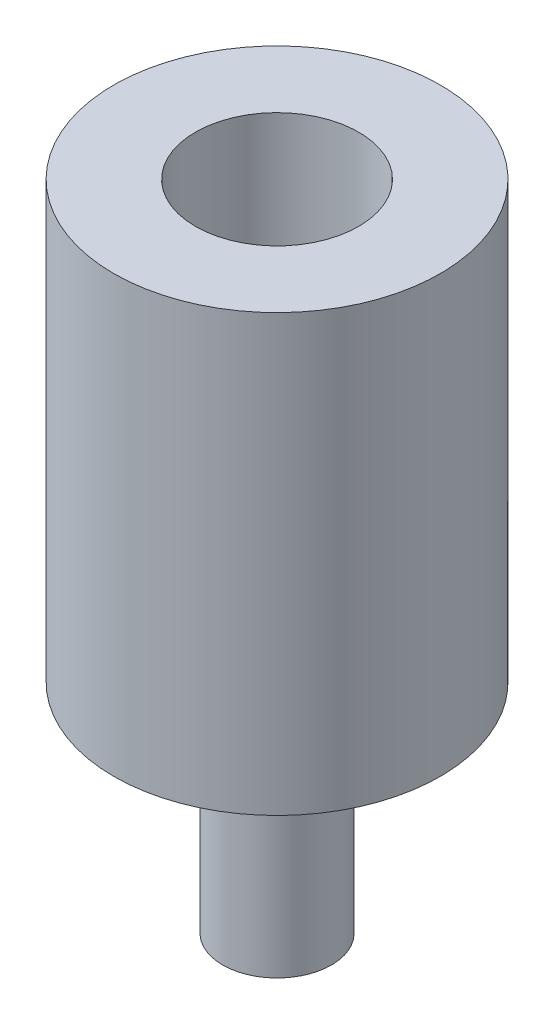
SolidWorks part; units mm, degrees
ref_plane "Front Plane" through (0, 0, 0) normal (0, 0, 1) x (1, 0, 0)
ref_plane "Top Plane" through (0, 0, 0) normal (0, 1, 0) x (1, 0, 0)
ref_plane "Right Plane" through (0, 0, 0) normal (1, 0, 0) x (0, 0, -1)
sketch "Sketch1" plane through (0, 0, 0) normal (0, 1, 0) x (1, 0, 0)
  circle A0 centre (0, 0) radius 2.5
  dimension "D1" = 5
extrude "Boss-Extrude2" add sketch "Sketch1" along normal blind 10
ref_plane "Plane1" through (0, 10, 0) normal (0, 1, 0) x (1, 0, 0)
sketch "Sketch2" plane through (0, 10, 0) normal (0, 1, 0) x (1, 0, 0)
  circle A0 centre (0, 0) radius 7.5
  dimension "D1" = 15
extrude "Boss-Extrude3" add sketch "Sketch2" along normal blind 20
sketch "Sketch3" plane through (0, 30, 0) normal (0, 1, 0) x (1, 0, 0)
  circle A0 centre (0, 0) radius 3.75
  dimension "D1" = 7.5
extrude "Cut-Extrude1" cut sketch "Sketch3" against normal blind 14
